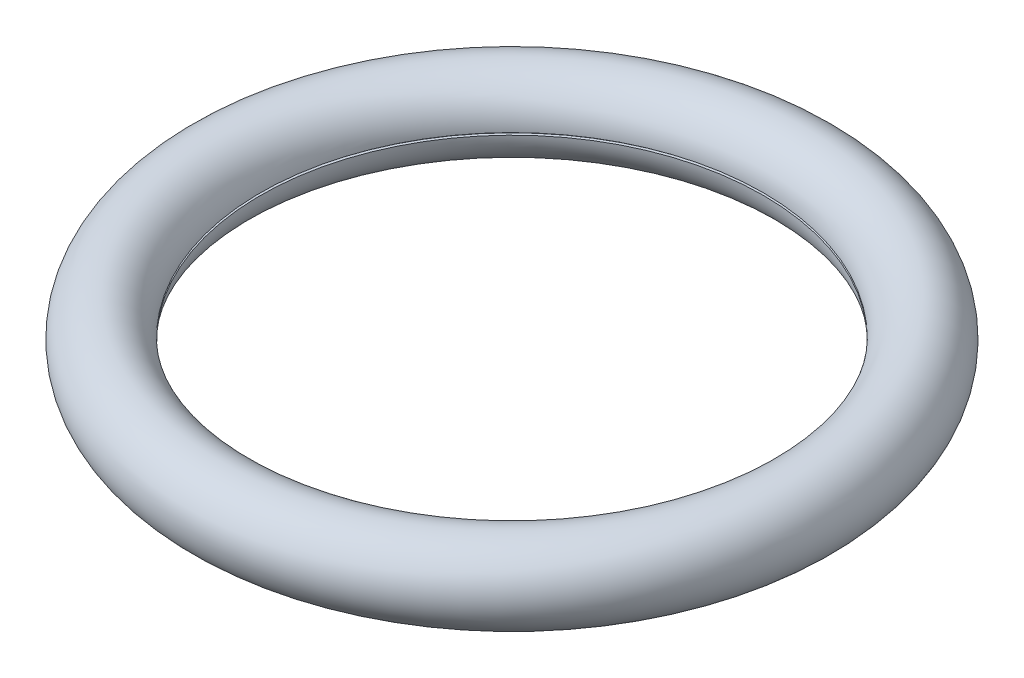
SolidWorks part; units mm, degrees
ref_plane "Front Plane" through (0, 0, 0) normal (0, 0, 1) x (1, 0, 0)
ref_plane "Top Plane" through (0, 0, 0) normal (0, 1, 0) x (1, 0, 0)
ref_plane "Right Plane" through (0, 0, 0) normal (1, 0, 0) x (0, 0, -1)
sketch "Sketch1" plane through (0, 0, 0) normal (0, 0, 1) x (1, 0, 0)
  line L0 (0, 3.175) -> (0, -3.175) construction
  line L1 (0, 3.175) -> (101.6, 3.175) construction
  line L2 (101.6, 3.175) -> (101.6, -3.175) construction
  line L3 (101.6, -3.175) -> (0, -3.175) construction
  circle A1 centre (101.6, 0) radius 12.7
  circle A2 centre (101.6, 0) radius 13.7
  point P6 (0, 0)
  dimension "D1" = 25.4
  dimension "D4" = 1
  dimension "D2" = 101.6
  dimension "D3" = 6.35
revolve "Revolve1" add sketch "Sketch1" angle 360 about L0
sketch "Sketch3" plane through (0, 0, 0) normal (0, 1, 0) x (1, 0, 0)
  line L0 (0, 38.1) -> (0, -38.1) construction
  line L1 (0, -19.05) -> (0, 19.05) construction
  line L2 (-93.3256, 19.05) -> (93.3256, 19.05) construction
  line L3 (93.3256, 19.05) -> (93.3256, -19.05) construction
  line L4 (93.3256, -19.05) -> (-93.3256, -19.05) construction
  line L5 (-93.3256, -19.05) -> (-93.3256, 19.05) construction
  line L6 (0, 142.903) -> (0, -142.903) construction
  line L7 (-19.05, -93.3256) -> (19.05, -93.3256) construction
  circle A0 centre (0, 0) radius 107.95
  arc A4 (27.7576, -91.1158) -> (91.1158, -27.7576) centre (0, 0) ccw
  arc A5 (-81.6387, 23.6682) -> (81.6387, 23.6682) centre (0, -200.025) cw
  arc A6 (19.6045, -84.2669) -> (84.2669, -19.6045) centre (93.3256, -93.3256) cw
  arc A7 (-84.2669, -19.6045) -> (-19.6045, -84.2669) centre (-93.3256, -93.3256) cw
  arc A8 (89.8026, 31.75) -> (-89.8026, 31.75) centre (0, 0) ccw
  arc A9 (-91.1158, -27.7576) -> (-27.7576, -91.1158) centre (0, 0) ccw
  arc A10 (84.2669, -19.6045) -> (91.1158, -27.7576) centre (85.0414, -25.9071) cw
  arc A11 (27.7576, -91.1158) -> (19.6045, -84.2669) centre (25.9071, -85.0414) cw
  arc A12 (-27.7576, -91.1158) -> (-19.6045, -84.2669) centre (-25.9071, -85.0414) ccw
  arc A13 (-84.2669, -19.6045) -> (-91.1158, -27.7576) centre (-85.0414, -25.9071) ccw
  arc A14 (81.6387, 23.6682) -> (89.8026, 31.75) centre (83.8157, 29.6333) ccw
  arc A15 (-81.6387, 23.6682) -> (-89.8026, 31.75) centre (-83.8157, 29.6333) cw
  point P7 (0, 0)
  point P10 (0, 38.1)
  point P11 (0, 0)
  point P14 (0, 19.05)
  point P15 (0, 38.1)
  point P20 (0, 0)
  point P24 (0, -93.3256)
  dimension "D1" = 76.2
  dimension "D2" = 190.5
  dimension "D3" = 215.9
  dimension "D4" = 38.1
  dimension "D6" = 6.35
  dimension "D5" = 38.1
extrude "Cut-Extrude1" cut sketch "Sketch3" against normal mid plane 0.1562 contours A5 A14 A8 A15
sketch "Sketch4" plane through (0, 0, 0) normal (0, 1, 0) x (1, 0, 0)
  circle A0 centre (0, 0) radius 107.95
  dimension "D1" = 215.9
extrude "Cut-Extrude2" cut sketch "Sketch4" against normal mid plane 0.7937
